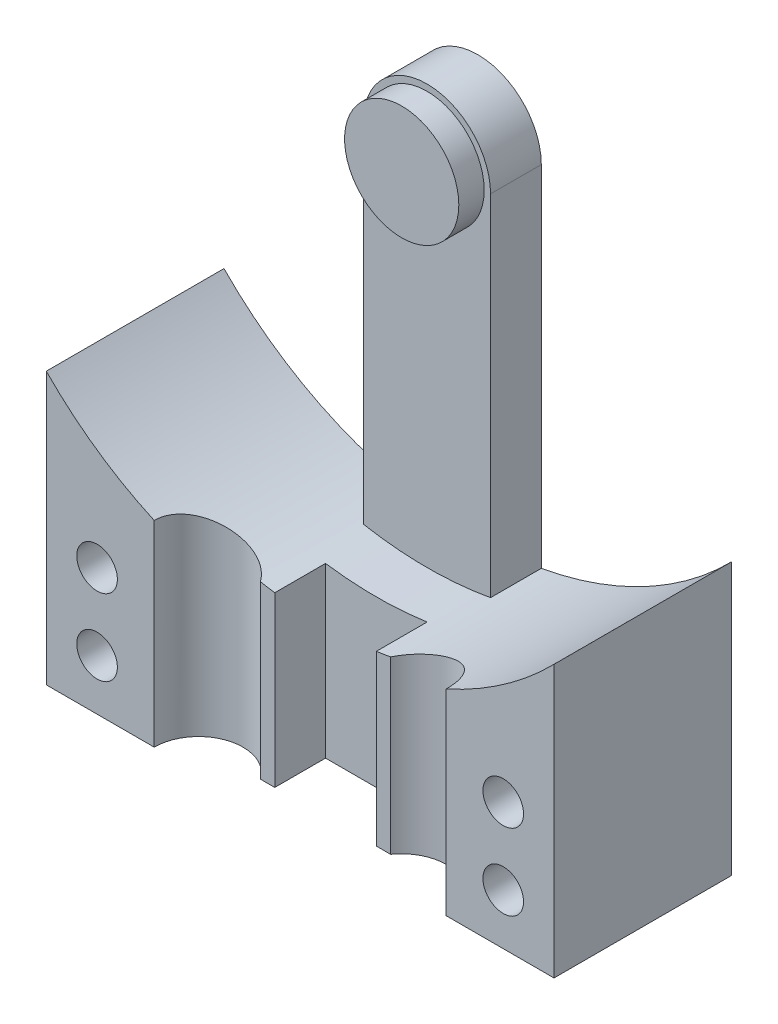
SolidWorks part; units mm, degrees
ref_plane "Front Plane" through (0, 0, 0) normal (0, 0, 1) x (1, 0, 0)
ref_plane "Top Plane" through (0, 0, 0) normal (0, 1, 0) x (1, 0, 0)
ref_plane "Right Plane" through (0, 0, 0) normal (1, 0, 0) x (0, 0, -1)
sketch "Sketch1" plane through (0, 0, 0) normal (0, 0, 1) x (1, 0, 0)
  line L0 (0, -14) -> (10, -14)
  line L1 (10, -14) -> (10, -20.5)
  line L2 (10, -20.5) -> (-10, -20.5)
  line L3 (-10, -20.5) -> (-10, -14)
  line L4 (-10, -14) -> (0, -14)
  line L5 (-10, -14) -> (-10, -9.798)
  line L6 (10, -14) -> (10, -9.798)
  circle A0 centre (0, 0) radius 12
  circle A2 centre (0, 0) radius 14
extrude "Boss-Extrude1" add sketch "Sketch1" along normal blind 7
sketch "Sketch2" plane through (0, 0, 0) normal (0, 0, 1) x (1, 0, 0)
  line L0 (0, 0) -> (0, -20.5) construction
  line L1 (0, 0) -> (2.5, 0) construction
  line L2 (0, 0) -> (-2.5, 0) construction
  line L3 (-2.5, 0) -> (-2.5, -20.5)
  line L5 (-2.5, -20.5) -> (2.5, -20.5)
  line L6 (2.5, -20.5) -> (2.5, 0)
  line L7 (10, -20.5) -> (-10, -20.5) construction
  arc A1 (2.5, 0) -> (-2.5, 0) centre (0, 0) ccw
extrude "Boss-Extrude2" add sketch "Sketch2" along normal blind 2
sketch "Sketch3" plane through (0, 0, 0) normal (0, 0, 1) x (1, 0, 0)
  circle A0 centre (0, 0) radius 2.25
extrude "Boss-Extrude3" add sketch "Sketch3" along normal blind 1 from offset 2
sketch "Sketch4" plane through (0, 0, 0) normal (0, 0, 1) x (1, 0, 0)
  line L0 (0, -15.5) -> (0, -18.5) construction
  line L1 (0, -15.5) -> (0, -14) construction
  line L2 (0, -15.5) -> (8, -15.5) construction
  line L3 (0, -15.5) -> (-8, -15.5) construction
  line L5 (0, -18.5) -> (8, -18.5) construction
  line L6 (0, -18.5) -> (-8, -18.5) construction
  arc A0 (-2.5, -13.775) -> (2.5, -13.775) centre (0, 0) ccw construction
  circle A1 centre (-8, -15.5) radius 0.8
  circle A2 centre (8, -15.5) radius 0.8
  circle A3 centre (-8, -18.5) radius 0.8
  circle A4 centre (8, -18.5) radius 0.8
extrude "Screw Holes" cut sketch "Sketch4" along normal through all
sketch "Sketch6" plane through (0, 0, 0) normal (0, 1, 0) x (1, 0, 0)
  line L0 (0, -7) -> (4, -7) construction
  line L1 (10, -7) -> (-10, -7) construction
  line L2 (0, -7) -> (-4, -7) construction
  line L3 (0, -7) -> (-4, -7) construction
  line L7 (0, -7) -> (4, -7) construction
  circle A0 centre (-4, -7) radius 1.75
  circle A1 centre (4, -7) radius 1.75
extrude "Cable Tubes" cut sketch "Sketch6" along normal blind 18.5 from offset 20.5 offset against normal yes
sketch "Sketch7" plane through (0, 0, 0) normal (0, 1, 0) x (1, 0, 0)
  line L0 (-3, -6) -> (-2, -6)
  line L1 (-2, -6) -> (-2, -4)
  line L2 (-2, -4) -> (2, -4)
  line L3 (2, -4) -> (2, -6)
  line L4 (2, -6) -> (3, -6)
  line L5 (-3, -7) -> (3, -7)
  line L6 (3, -7) -> (3, -6)
  line L8 (-3, -6) -> (-3, -7)
extrude "Wire Canals" cut sketch "Sketch7" along normal blind 7.5 from offset 20.5
